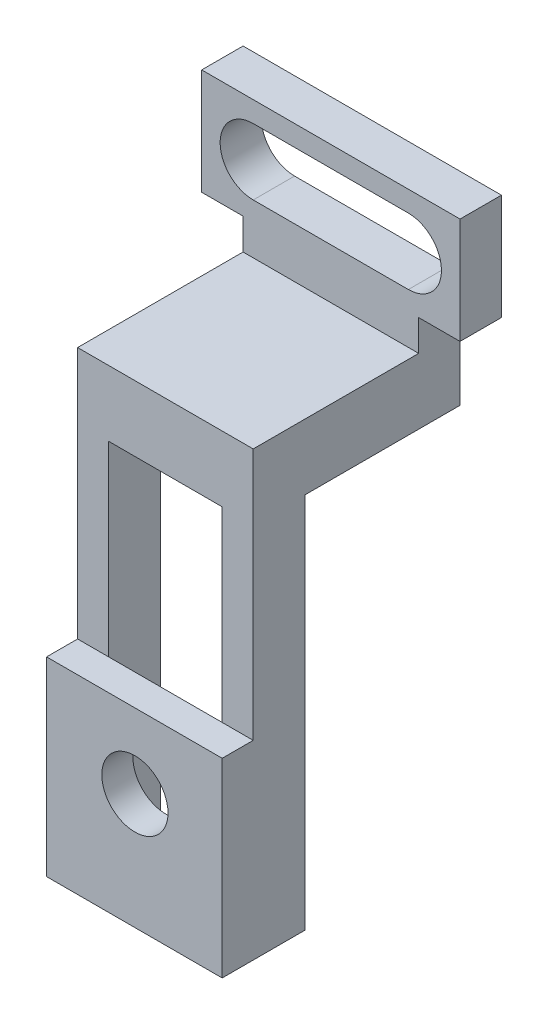
SolidWorks part; units mm, degrees
ref_plane "Front Plane" through (0, 0, 0) normal (0, 0, 1) x (1, 0, 0)
ref_plane "Top Plane" through (0, 0, 0) normal (0, 1, 0) x (1, 0, 0)
ref_plane "Right Plane" through (0, 0, 0) normal (1, 0, 0) x (0, 0, -1)
sketch "Sketch2" plane through (0, 0, 0) normal (0, 0, 1) x (1, 0, 0)
  line L0 (-6.5238, 2.0903) -> (0.8762, 2.0903) construction
  line L1 (-6.5238, 7.3453) -> (6.8762, 7.3453)
  line L2 (-6.5238, 7.3453) -> (-6.5238, -3.1647)
  line L3 (-6.5238, -3.1647) -> (6.8762, -3.1647)
  line L4 (6.8762, 7.3453) -> (6.8762, -3.1647)
  circle A0 centre (0.8762, 2.0903) radius 3.2
  dimension "D4" = 6.4
  dimension "D1" = 13.4
  dimension "D2" = 10.51
  dimension "D3" = 7.4
extrude "Boss-Extrude1" add sketch "Sketch2" along normal blind 3
sketch "Sketch4" plane through (0, 0, 3) normal (0, 0, 1) x (1, 0, 0)
  line L0 (0.8762, -1.1097) -> (0.8762, -9.1097) construction
  line L2 (-6.5238, -3.1647) -> (6.8832, -3.1647)
  line L3 (-6.5238, -3.1647) -> (-6.5238, -9.1097)
  line L4 (-6.5238, -9.1097) -> (6.8832, -9.1097)
  line L5 (6.8832, -3.1647) -> (6.8832, -9.1097)
  circle A0 centre (0.8762, 2.0903) radius 3.2 construction
  dimension "D1" = 8
extrude "Boss-Extrude3" add sketch "Sketch4" against normal blind 3
sketch "Sketch5" plane through (0, 0, 0) normal (0, 0, -1) x (-1, 0, 0)
  line L0 (-0.8762, -1.1097) -> (-0.8762, -6.0797) construction
  circle A0 centre (-0.8762, 2.0903) radius 3.2 construction
  circle A1 centre (-0.8762, -6.0797) radius 1.65
  dimension "D2" = 3.3
  dimension "D1" = 4.97
extrude "Boss-Extrude4" add sketch "Sketch5" along normal blind 3
sketch "Sketch6" plane through (-6.5238, 0, 0) normal (-1, 0, 0) x (0, 0, 1)
  line L0 (0, -7.4091) -> (0, 7.4091) construction
  line L1 (0, 7.3453) -> (3, 7.3453)
  line L2 (0, 7.3453) -> (0, -9.1097)
  line L3 (0, -9.1097) -> (3, -9.1097)
  line L4 (3, 7.3453) -> (3, -9.1097)
  line L5 (3, 7.3453) -> (0, 7.3453) construction
extrude "Boss-Extrude5" add sketch "Sketch6" along normal blind 4
sketch "Sketch7" plane through (0, 0, 0) normal (0, 0, -1) x (-1, 0, 0)
  line L0 (10.5238, -9.1097) -> (-6.8832, -9.1097) construction
  line L1 (10.5238, 7.3453) -> (9.5238, 7.3453)
  line L2 (10.5238, 7.3453) -> (10.5238, -9.1097)
  line L3 (10.5238, -9.1097) -> (9.5238, -9.1097)
  line L4 (9.5238, 7.3453) -> (9.5238, -9.1097)
  dimension "D1" = 1
extrude "Boss-Extrude6" add sketch "Sketch7" along normal blind 5
sketch "Sketch11" plane through (0, 7.3453, 0) normal (0, 1, 0) x (1, 0, 0)
  line L0 (6.8762, -3) -> (-10.5238, -3) construction
  line L1 (-10.5238, 5) -> (-9.5355, 5)
  line L2 (-10.5238, 5) -> (-10.5238, -3)
  line L3 (-10.5238, -3) -> (-9.5355, -3)
  line L4 (-9.5355, 5) -> (-9.5355, -3)
extrude "Boss-Extrude8" add sketch "Sketch11" along normal blind 6
sketch "Sketch16" plane through (0, 0, -5) normal (0, 0, -1) x (-1, 0, 0)
  line L0 (10.5238, -9.1097) -> (10.5238, 13.3453) construction
  line L1 (9.5355, 13.3453) -> (10.5238, 13.3453)
  line L2 (9.5355, 13.3453) -> (9.5355, 7.3453)
  line L3 (9.5355, 7.3453) -> (10.5238, 7.3453)
  line L4 (10.5238, 13.3453) -> (10.5238, 7.3453)
  dimension "D1" = 6
extrude "Boss-Extrude12" add sketch "Sketch16" along normal blind 6
sketch "Sketch17" plane through (-10.5238, 0, 0) normal (-1, 0, 0) x (0, 0, 1)
  line L0 (-11, 7.3453) -> (-5, -9.1097)
  line L1 (-5, -9.1097) -> (-5, 7.3453)
  line L2 (-5, 7.3453) -> (-11, 7.3453)
extrude "Boss-Extrude13" add sketch "Sketch17" against normal blind 1
sketch "Sketch20" plane through (-10.5238, 0, 0) normal (-1, 0, 0) x (0, 0, 1)
  line L1 (-11, 13.3453) -> (-5, 13.3453)
  line L2 (-11, 13.3453) -> (-11, 11.3212)
  line L3 (-11, 11.3212) -> (-5, 11.3212)
  line L4 (-5, 13.3453) -> (-5, 11.3212)
  dimension "D1" = 6
extrude "Boss-Extrude15" add sketch "Sketch20" along normal blind 20
sketch "Sketch21" plane through (0, 11.3212, 0) normal (0, -1, 0) x (1, 0, 0)
  line L0 (-30.5238, -8) -> (-6.5602, -8) construction
  line L1 (-30.5238, -11) -> (-30.5238, -5) construction
  line L2 (-20.5238, -5) -> (-20.5238, -12.6331) construction
  line L3 (-30.5238, -5) -> (-10.5238, -5) construction
  line L4 (-27.1602, -8) -> (-13.5238, -8) construction
  line L5 (-27.1602, -6.4) -> (-13.5238, -6.4)
  line L6 (-27.1602, -9.6) -> (-13.5238, -9.6)
  line L7 (-10.5238, -11) -> (-10.5238, -5) construction
  arc A0 (-27.1602, -6.4) -> (-27.1602, -9.6) centre (-27.1602, -8) ccw
  arc A1 (-13.5238, -9.6) -> (-13.5238, -6.4) centre (-13.5238, -8) ccw
  point P10 (-20.342, -8)
  dimension "D1" = 3.2
  dimension "D2" = 3
extrude "Cut-Extrude3" cut sketch "Sketch21" against normal through all
sketch "Sketch22" plane through (6.8762, 0, 0) normal (1, 0, 0) x (0, 0, -1)
  line L1 (-3, 7.3453) -> (0, 7.3453)
  line L2 (-3, 7.3453) -> (-3, -9.1097)
  line L3 (-3, -9.1097) -> (0, -9.1097)
  line L4 (0, 7.3453) -> (0, -9.1097)
extrude "Boss-Extrude16" add sketch "Sketch22" along normal blind 0.44
sketch "Sketch23" plane through (0, 0, 0) normal (0, 0, -1) x (-1, 0, 0)
  line L0 (9.5238, -9.1097) -> (-7.3162, -9.1097) construction
  line L1 (-7.3162, 7.3453) -> (-6.3162, 7.3453)
  line L2 (-7.3162, 7.3453) -> (-7.3162, -9.1097)
  line L3 (-7.3162, -9.1097) -> (-6.3162, -9.1097)
  line L4 (-6.3162, 7.3453) -> (-6.3162, -9.1097)
  dimension "D1" = 1
extrude "Boss-Extrude17" add sketch "Sketch23" along normal blind 3
sketch "Sketch24" plane through (0, 11.3212, 0) normal (0, -1, 0) x (1, 0, 0)
  line L0 (-30.5238, -5) -> (-10.5238, -5)
  line L1 (-10.5238, -5) -> (-10.5238, 3)
  line L2 (-10.5238, 3) -> (-30.5238, -5)
  dimension "D1" = 8
extrude "Boss-Extrude18" add sketch "Sketch24" against normal blind 2
sketch "Sketch25" plane through (0, 13.3453, 0) normal (0, 1, 0) x (1, 0, 0)
  line L1 (-30.5238, 11) -> (-10.4857, 11)
  line L2 (-30.5238, 11) -> (-30.5238, -4.7072)
  line L3 (-30.5238, -4.7072) -> (-10.4857, -4.7072)
  line L4 (-10.4857, 11) -> (-10.4857, -4.7072)
extrude "Cut-Extrude4" cut sketch "Sketch25" against normal blind 10
sketch "Sketch26" plane through (7.3162, 0, 0) normal (1, 0, 0) x (0, 0, -1)
  line L1 (-3, 7.3453) -> (3, 7.3453)
  line L2 (-3, 7.3453) -> (-3, -9.1097)
  line L3 (-3, -9.1097) -> (3, -9.1097)
  line L4 (3, 7.3453) -> (3, -9.1097)
extrude "Boss-Extrude19" add sketch "Sketch26" along normal blind 2
sketch "Sketch27" plane through (0, 0, -3) normal (0, 0, -1) x (-1, 0, 0)
  line L1 (-9.3162, 7.3453) -> (-6.3162, 7.3453)
  line L2 (-9.3162, 7.3453) -> (-9.3162, -9.1097)
  line L3 (-9.3162, -9.1097) -> (-6.3162, -9.1097)
  line L4 (-6.3162, 7.3453) -> (-6.3162, -9.1097)
extrude "Boss-Extrude20" add sketch "Sketch27" along normal blind 2
sketch "Sketch28" plane through (-10.5238, 0, 0) normal (-1, 0, 0) x (0, 0, 1)
  line L0 (-11, 13.3453) -> (-11, 7.3453)
  line L1 (-11, 7.3453) -> (-5, -9.1097)
  line L2 (-5, -9.1097) -> (3, -9.1097)
  line L3 (3, -9.1097) -> (3, 13.3453)
  line L4 (3, 13.3453) -> (-11, 13.3453)
extrude "Boss-Extrude21" add sketch "Sketch28" along normal blind 3
sketch "Sketch29" plane through (0, 13.3453, 0) normal (0, 1, 0) x (1, 0, 0)
  line L1 (-13.5238, 11) -> (-9.5355, 11)
  line L2 (-13.5238, 11) -> (-13.5238, -3)
  line L3 (-13.5238, -3) -> (-9.5355, -3)
  line L4 (-9.5355, 11) -> (-9.5355, -3)
extrude "Boss-Extrude22" add sketch "Sketch29" along normal blind 3
sketch "Sketch30" plane through (0, 0, -11) normal (0, 0, -1) x (-1, 0, 0)
  line L1 (9.5355, 16.3453) -> (13.5238, 16.3453)
  line L2 (9.5355, 16.3453) -> (9.5355, 7.3453)
  line L3 (9.5355, 7.3453) -> (13.5238, 7.3453)
  line L4 (13.5238, 16.3453) -> (13.5238, 7.3453)
extrude "Boss-Extrude23" add sketch "Sketch30" along normal blind 4
sketch "Sketch31" plane through (-13.5238, 0, 0) normal (-1, 0, 0) x (0, 0, 1)
  line L1 (-15, 16.3453) -> (-11, 16.3453)
  line L2 (-15, 16.3453) -> (-15, 7.3453)
  line L3 (-15, 7.3453) -> (-11, 7.3453)
  line L4 (-11, 16.3453) -> (-11, 7.3453)
extrude "Boss-Extrude24" add sketch "Sketch31" along normal blind 12
sketch "Sketch32" plane through (0, 16.3453, 0) normal (0, 1, 0) x (1, 0, 0)
  line L1 (-25.5238, 15) -> (-13.5238, 15)
  line L2 (-25.5238, 15) -> (-25.5238, 11)
  line L3 (-25.5238, 11) -> (-13.5238, 11)
  line L4 (-13.5238, 15) -> (-13.5238, 11)
extrude "Boss-Extrude25" add sketch "Sketch32" along normal blind 12
sketch "Sketch33" plane through (0, 0, -15) normal (0, 0, -1) x (-1, 0, 0)
  line L0 (19.5238, 28.3453) -> (19.5238, 5.7133) construction
  line L1 (13.5238, 28.3453) -> (25.5238, 28.3453) construction
  line L2 (19.5238, 28.3453) -> (19.5238, 17.0293) construction
  line L3 (22.7238, 28.3453) -> (22.7238, 17.0293)
  line L4 (16.3238, 28.3453) -> (16.3238, 17.0293)
  arc A0 (22.7238, 28.3453) -> (16.3238, 28.3453) centre (19.5238, 28.3453) ccw
  arc A1 (16.3238, 17.0293) -> (22.7238, 17.0293) centre (19.5238, 17.0293) ccw
  point P4 (19.5238, 22.6873)
  dimension "D1" = 3.2
sketch "Sketch34" plane through (0, 28.3453, 0) normal (0, 1, 0) x (1, 0, 0)
  line L1 (-25.5238, 15) -> (-13.5238, 15)
  line L2 (-25.5238, 15) -> (-25.5238, 11)
  line L3 (-25.5238, 11) -> (-13.5238, 11)
  line L4 (-13.5238, 15) -> (-13.5238, 11)
extrude "Boss-Extrude26" add sketch "Sketch34" along normal blind 10
extrude "Cut-Extrude5" cut sketch "Sketch33" against normal blind 10
sketch "Sketch35" plane through (-9.5355, 0, 0) normal (1, 0, 0) x (0, 0, -1)
  line L1 (-3, 7.3453) -> (19.0491, 7.3453)
  line L2 (-3, 7.3453) -> (-3, 39.0923)
  line L3 (-3, 39.0923) -> (19.0491, 39.0923)
  line L4 (19.0491, 7.3453) -> (19.0491, 39.0923)
extrude "Cut-Extrude6" cut sketch "Sketch35" against normal blind 40
sketch "Sketch36" plane through (-13.5238, 0, 0) normal (-1, 0, 0) x (0, 0, 1)
  line L0 (-5, -9.1097) -> (-5, 7.3453)
  line L1 (-11, 7.3453) -> (3, 7.3453) construction
  line L2 (-5, 7.3453) -> (-11, 7.3453)
  line L3 (-11, 7.3453) -> (-5, -9.1097)
extrude "Cut-Extrude7" cut sketch "Sketch36" against normal blind 40
sketch "Sketch37" plane through (0, 7.3453, 0) normal (0, 1, 0) x (1, 0, 0)
  line L0 (-13.5238, 5) -> (-13.5238, -3)
  line L1 (-13.5238, -3) -> (9.3162, -3)
  line L2 (9.3162, -3) -> (9.3162, 5)
  line L3 (9.3162, 5) -> (6.3162, 5)
  line L4 (6.3162, 5) -> (6.3162, 0)
  line L5 (6.3162, 0) -> (-9.5238, 0)
  line L6 (-9.5238, 0) -> (-9.5238, 5)
  line L7 (-9.5238, 5) -> (-13.5238, 5)
extrude "Boss-Extrude27" add sketch "Sketch37" along normal blind 20
sketch "Sketch38" plane through (0, 0, 0) normal (0, 0, -1) x (-1, 0, 0)
  line L0 (-0.8762, 5.2903) -> (-0.8762, 9.2903) construction
  line L1 (-6.3162, -9.1097) -> (-6.3162, 27.3453) construction
  line L2 (-6.3162, 9.2903) -> (9.5238, 9.2903)
  line L3 (-6.3162, 9.2903) -> (-6.3162, 27.3453)
  line L4 (-6.3162, 27.3453) -> (9.5238, 27.3453)
  line L5 (9.5238, 9.2903) -> (9.5238, 27.3453)
  circle A0 centre (-0.8762, 2.0903) radius 3.2 construction
  dimension "D1" = 4
extrude "Cut-Extrude8" cut sketch "Sketch38" against normal blind 20
sketch "Sketch40" plane through (0, 0, -5) normal (0, 0, -1) x (-1, 0, 0)
  line L0 (9.5238, -9.1097) -> (-6.3162, -9.1097) construction
  line L1 (13.5238, 27.3453) -> (4.6638, 27.3453)
  line L2 (13.5238, 27.3453) -> (13.5238, -9.1097)
  line L3 (13.5238, -9.1097) -> (4.6638, -9.1097)
  line L4 (4.6638, 27.3453) -> (4.6638, -9.1097)
  circle A0 centre (-0.8762, 2.0903) radius 3.2 construction
  dimension "D1" = 5.54
extrude "Cut-Extrude9" cut sketch "Sketch40" against normal blind 10
sketch "Sketch41" plane through (-4.6638, 0, 0) normal (-1, 0, 0) x (0, 0, 1)
  line L1 (3, -9.1097) -> (-5, -9.1097)
  line L2 (3, -9.1097) -> (3, 27.3453)
  line L3 (3, 27.3453) -> (-5, 27.3453)
  line L4 (-5, -9.1097) -> (-5, 27.3453)
extrude "Boss-Extrude28" add sketch "Sketch41" along normal blind 3
sketch "Sketch42" plane through (0, 27.3453, 0) normal (0, 1, 0) x (1, 0, 0)
  line L1 (-7.6638, 5) -> (9.3162, 5)
  line L2 (-7.6638, 5) -> (-7.6638, -3)
  line L3 (-7.6638, -3) -> (9.3162, -3)
  line L4 (9.3162, 5) -> (9.3162, -3)
extrude "Boss-Extrude29" add sketch "Sketch42" along normal blind 6.35
sketch "Sketch43" plane through (0, 0, -5) normal (0, 0, -1) x (-1, 0, 0)
  line L0 (-6.3162, 27.3453) -> (-10.9112, 27.3453) construction
  line L1 (-9.3162, 33.6953) -> (-9.3162, -9.1097) construction
  line L2 (-9.3162, 27.3453) -> (7.6638, 27.3453)
  line L3 (-9.3162, 27.3453) -> (-9.3162, 33.6953)
  line L4 (-9.3162, 33.6953) -> (7.6638, 33.6953)
  line L5 (7.6638, 27.3453) -> (7.6638, 33.6953)
extrude "Boss-Extrude30" add sketch "Sketch43" along normal blind 15
sketch "Sketch44" plane through (0, 33.6953, 0) normal (0, 1, 0) x (1, 0, 0)
  line L0 (9.3162, -3) -> (9.3162, 20) construction
  line L1 (-7.6638, 20) -> (9.3162, 20)
  line L2 (-7.6638, 20) -> (-7.6638, 16)
  line L3 (-7.6638, 16) -> (9.3162, 16)
  line L4 (9.3162, 20) -> (9.3162, 16)
  dimension "D1" = 4
extrude "Boss-Extrude31" add sketch "Sketch44" along normal blind 9.2
sketch "Sketch45" plane through (9.3162, 0, 0) normal (1, 0, 0) x (0, 0, -1)
  line L0 (20, 42.8953) -> (20, 27.3453) construction
  line L1 (16, 42.8953) -> (20, 42.8953)
  line L2 (16, 42.8953) -> (16, 33.6953)
  line L3 (16, 33.6953) -> (20, 33.6953)
  line L4 (20, 42.8953) -> (20, 33.6953)
  dimension "D1" = 9.2
extrude "Boss-Extrude32" add sketch "Sketch45" along normal blind 4
sketch "Sketch46" plane through (-7.6638, 0, 0) normal (-1, 0, 0) x (0, 0, 1)
  line L0 (-20, 27.3453) -> (-20, 42.8953) construction
  line L1 (-16, 33.6953) -> (-20, 33.6953)
  line L2 (-16, 33.6953) -> (-16, 42.8953)
  line L3 (-16, 42.8953) -> (-20, 42.8953)
  line L4 (-20, 33.6953) -> (-20, 42.8953)
extrude "Boss-Extrude33" add sketch "Sketch46" along normal blind 4
sketch "Sketch47" plane through (0, 0, -20) normal (0, 0, -1) x (-1, 0, 0)
  line L0 (-13.3162, 38.2953) -> (13.7115, 38.2953) construction
  line L1 (-13.3162, 33.6953) -> (-13.3162, 42.8953) construction
  line L2 (-8.3162, 38.2953) -> (6.6838, 38.2953) construction
  line L3 (-8.3162, 41.4953) -> (6.6838, 41.4953)
  line L4 (-8.3162, 35.0953) -> (6.6838, 35.0953)
  arc A0 (-8.3162, 41.4953) -> (-8.3162, 35.0953) centre (-8.3162, 38.2953) ccw
  arc A1 (6.6838, 35.0953) -> (6.6838, 41.4953) centre (6.6838, 38.2953) ccw
  point P6 (-0.8162, 38.2953)
  dimension "D1" = 3.2
  dimension "D2" = 15
  dimension "D3" = 5
extrude "Cut-Extrude11" cut sketch "Sketch47" against normal blind 4
sketch "Sketch49" plane through (-7.6638, 0, 0) normal (-1, 0, 0) x (0, 0, 1)
  line L0 (-16, 33.6953) -> (3, 33.6953) construction
  line L1 (3, 9.2903) -> (0, 9.2903)
  line L2 (3, 9.2903) -> (3, 33.6953)
  line L3 (3, 33.6953) -> (0, 33.6953)
  line L4 (0, 9.2903) -> (0, 33.6953)
extrude "Cut-Extrude13" cut sketch "Sketch49" against normal blind 24
sketch "Sketch50" plane through (0, 0, -20) normal (0, 0, -1) x (-1, 0, 0)
  line L1 (-13.3162, 33.6953) -> (11.6638, 33.6953)
  line L2 (-13.3162, 33.6953) -> (-13.3162, 42.8953)
  line L3 (-13.3162, 42.8953) -> (11.6638, 42.8953)
  line L4 (11.6638, 33.6953) -> (11.6638, 42.8953)
extrude "Cut-Extrude14" cut sketch "Sketch50" against normal blind 10
sketch "Sketch51" plane through (0, 33.6953, 0) normal (0, 1, 0) x (1, 0, 0)
  line L0 (9.3162, 0) -> (9.3162, 20) construction
  line L1 (-7.6638, 20) -> (9.3162, 20)
  line L2 (-7.6638, 20) -> (-7.6638, 16)
  line L3 (-7.6638, 16) -> (9.3162, 16)
  line L4 (9.3162, 20) -> (9.3162, 16)
  dimension "D1" = 4
extrude "Boss-Extrude34" add sketch "Sketch51" along normal blind 12.2
sketch "Sketch52" plane through (9.3162, 0, 0) normal (1, 0, 0) x (0, 0, -1)
  line L0 (16, 45.8953) -> (16, 33.6953) construction
  line L1 (16, 36.6953) -> (20, 36.6953)
  line L2 (16, 36.6953) -> (16, 45.8953)
  line L3 (16, 45.8953) -> (20, 45.8953)
  line L4 (20, 36.6953) -> (20, 45.8953)
  dimension "D1" = 9.2
extrude "Boss-Extrude35" add sketch "Sketch52" along normal blind 4
sketch "Sketch53" plane through (-7.6638, 0, 0) normal (-1, 0, 0) x (0, 0, 1)
  line L1 (-20, 45.8953) -> (-16, 45.8953)
  line L2 (-20, 45.8953) -> (-20, 36.6953)
  line L3 (-20, 36.6953) -> (-16, 36.6953)
  line L4 (-16, 45.8953) -> (-16, 36.6953)
extrude "Boss-Extrude36" add sketch "Sketch53" along normal blind 4
sketch "Sketch54" plane through (0, 0, -20) normal (0, 0, -1) x (-1, 0, 0)
  line L0 (-13.3162, 41.7437) -> (11.6638, 41.7437) construction
  line L1 (-13.3162, 36.6953) -> (-13.3162, 45.8953) construction
  line L2 (11.6638, 45.8953) -> (11.6638, 36.6953) construction
  line L3 (-8.3162, 41.7437) -> (6.6838, 41.7437) construction
  line L4 (-8.3162, 44.9437) -> (6.6838, 44.9437)
  line L5 (-8.3162, 38.5437) -> (6.6838, 38.5437)
  arc A0 (-8.3162, 44.9437) -> (-8.3162, 38.5437) centre (-8.3162, 41.7437) ccw
  arc A1 (6.6838, 38.5437) -> (6.6838, 44.9437) centre (6.6838, 41.7437) ccw
  point P8 (-0.8162, 41.7437)
  dimension "D1" = 3.2
  dimension "D3" = 5
  dimension "D2" = 15
extrude "Cut-Extrude15" cut sketch "Sketch54" against normal blind 4
sketch "Sketch55" plane through (0, 45.8953, 0) normal (0, 1, 0) x (1, 0, 0)
  line L1 (-11.6638, 20) -> (13.3162, 20)
  line L2 (-11.6638, 20) -> (-11.6638, 16)
  line L3 (-11.6638, 16) -> (13.3162, 16)
  line L4 (13.3162, 20) -> (13.3162, 16)
extrude "Boss-Extrude37" add sketch "Sketch55" along normal blind 1.05
